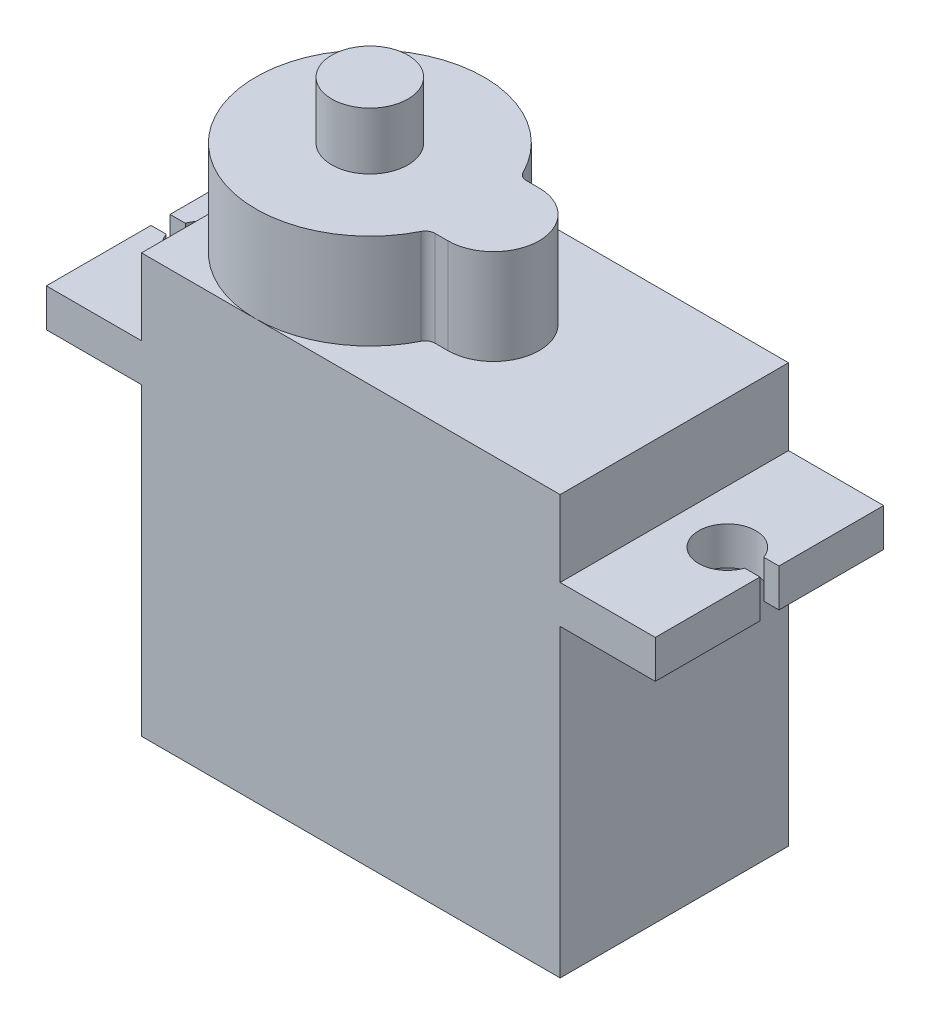
SolidWorks part; units mm, degrees
ref_plane "前视基准面" through (0, 0, 0) normal (0, 0, 1) x (1, 0, 0)
ref_plane "上视基准面" through (0, 0, 0) normal (0, 1, 0) x (1, 0, 0)
ref_plane "右视基准面" through (0, 0, 0) normal (1, 0, 0) x (0, 0, -1)
sketch "Sketch1" plane through (0, 0, 0) normal (0, 0, 1) x (1, 0, 0)
  line L0 (11, 7) -> (16, 7)
  line L1 (-11, -11) -> (11, -11)
  line L2 (-11, -11) -> (-11, 5)
  line L3 (-11, 11) -> (11, 11)
  line L4 (11, -11) -> (11, 5)
  line L5 (-11, -11) -> (11, 11) construction
  line L6 (-11, 11) -> (11, -11) construction
  line L7 (16, 7) -> (16, 5)
  line L8 (16, 5) -> (11, 5)
  line L9 (11, 7) -> (11, 11)
  line L10 (-11, 7) -> (-16, 7)
  line L11 (-16, 7) -> (-16, 5)
  line L12 (-16, 5) -> (-11, 5)
  line L13 (-11, 7) -> (-11, 11)
  point P0 (0, 0)
  dimension "D1" = 22
  dimension "D2" = 22
  dimension "D3" = 4
  dimension "D4" = 2
  dimension "D5" = 5
  dimension "D6" = 5
  dimension "D7" = 2
extrude "Boss-Extrude1" add sketch "Sketch1" against normal blind 12
sketch "Sketch2" plane through (0, 11, 0) normal (0, 1, 0) x (1, 0, 0)
  line L0 (4.2005, 6) -> (-49995.7995, 6) construction
  line L1 (0, 6.0354) -> (0, -49993.9646) construction
  line L2 (11, 0) -> (-11, 0) construction
  line L4 (1.4991, 8.4) -> (0.4991, 8.4)
  line L5 (1.4991, 3.6) -> (0.4991, 3.6)
  line L6 (-11, 12) -> (-11, 0) construction
  arc A0 (0.4991, 8.4) -> (0.4991, 3.6) centre (-5, 6) ccw
  arc A1 (1.4991, 3.6) -> (1.4991, 8.4) centre (1.4991, 6) ccw
  dimension "D1" = 12
  dimension "D2" = 4.8
  dimension "D3" = 1
extrude "Boss-Extrude2" add sketch "Sketch2" along normal blind 5
sketch "Sketch3" plane through (0, 7, 0) normal (0, 1, 0) x (1, 0, 0)
  line L0 (200004.2005, 6) -> (-249995.7995, 6) construction
  line L1 (15.2, 6.5) -> (16, 6.5)
  line L2 (16, 12) -> (16, 0) construction
  line L3 (16, 6.5) -> (16, 5.5)
  line L4 (16, 5.5) -> (15.2, 5.5)
  arc A0 (15.2, 6.5) -> (15.2, 5.5) centre (13.7858, 6) ccw
  dimension "D1" = 3
  dimension "D2" = 1
  dimension "D3" = 0.8
extrude "Cut-Extrude1" cut sketch "Sketch3" against normal through all both and the other way through all
mirror "Mirror1" about plane through (0, 0, 0) normal (1, 0, 0) of "Cut-Extrude1"
sketch "Sketch4" plane through (0, 16, 0) normal (0, 1, 0) x (1, 0, 0)
  circle A0 centre (-5, 6) radius 2
  dimension "D1" = 4
extrude "Boss-Extrude3" add sketch "Sketch4" along normal blind 3
fillet "Fillet1" radius 0.5 2 edges at (0.4991, 13.5, -8.4) (0.4991, 13.5, -3.6)
